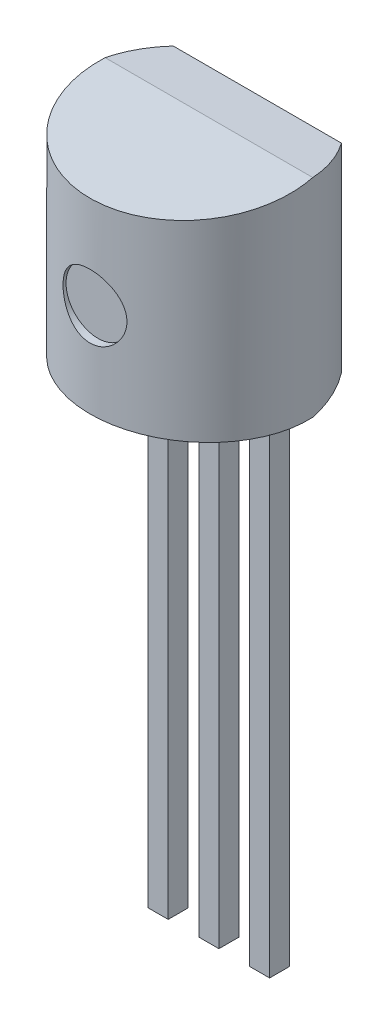
SolidWorks part; units mm, degrees
ref_plane "Front Plane" through (0, 0, 0) normal (0, 0, 1) x (1, 0, 0)
ref_plane "Top Plane" through (0, 0, 0) normal (0, 1, 0) x (1, 0, 0)
ref_plane "Right Plane" through (0, 0, 0) normal (1, 0, 0) x (0, 0, -1)
sketch "Sketch2" plane through (0, 0, 0) normal (0, 1, 0) x (1, 0, 0)
  line L0 (-2.6, 0) -> (2.6, 0) construction
  line L1 (-2.1054, 1.212) -> (2.1054, 1.212)
  line L2 (0, 0) -> (0, 1.212) construction
  arc A0 (-2.1054, 1.212) -> (2.1054, 1.212) centre (0, -0.354) ccw
  point P3 (0, 0)
  dimension "D1" = 4.19
  dimension "D2" = 5.2
  dimension "D3" = 2.27
extrude "Boss-Extrude1" add sketch "Sketch2" along normal mid plane 5.2
sketch "Sketch3" plane through (0, 2.6, 0) normal (0, 1, 0) x (1, 0, 0)
  line L0 (-2.6, 0) -> (2.6, 0) construction
  line L1 (-2.6, 0) -> (2.6, 0) construction
ref_plane "Plane1" through (0, 2.5803, -0.2257) normal (0, 0.9962, -0.0872) x (1, 0, 0)
ref_plane "Plane2" through (0, 2.5803, 0.2257) normal (0, 0.9962, 0.0872) x (1, 0, 0)
sketch "Sketch5" plane through (0, 2.5803, -0.2257) normal (0, 0.9962, -0.0872) x (1, 0, 0)
  line L1 (-4.9885, 2.0659) -> (6.8379, 2.0659)
  line L2 (-4.9885, 2.0659) -> (-4.9885, -3.5552)
  line L3 (-4.9885, -3.5552) -> (6.8379, -3.5552)
  line L4 (6.8379, 2.0659) -> (6.8379, -3.5552)
extrude "Cut-Extrude2" cut sketch "Sketch5" along normal through all
sketch "Sketch6" plane through (0, 2.5803, 0.2257) normal (0, 0.9962, 0.0872) x (1, 0, 0)
  line L1 (-5.588, 1.1618) -> (6.1027, 1.1618)
  line L2 (-5.588, 1.1618) -> (-5.588, -6.0928)
  line L3 (-5.588, -6.0928) -> (6.1027, -6.0928)
  line L4 (6.1027, 1.1618) -> (6.1027, -6.0928)
extrude "Cut-Extrude3" cut sketch "Sketch6" along normal blind 5.2
mirror "Mirror1" about plane through (0, 0, 0) normal (0, 1, 0) of "Cut-Extrude3", "Cut-Extrude2"
ref_plane "Plane3" through (0, -2.6, 0) normal (0, -1, 0) x (-1, 0, 0)
sketch "Sketch7" plane through (0, -2.6, 0) normal (0, -1, 0) x (-1, 0, 0)
  line L0 (-2.6, 0) -> (2.6, 0) construction
  line L1 (-1.52, 0) -> (-1.02, 0)
  line L2 (-1.52, 0) -> (-1.52, 0.5)
  line L3 (-1.52, 0.5) -> (-1.02, 0.5)
  line L4 (-1.02, 0) -> (-1.02, 0.5)
  line L5 (0, 0) -> (0, 0.5) construction
  line L6 (-0.25, 0) -> (0.25, 0)
  line L7 (-0.25, 0) -> (-0.25, 0.5)
  line L8 (-0.25, 0.5) -> (0.25, 0.5)
  line L9 (0.25, 0) -> (0.25, 0.5)
  line L10 (1.02, 0) -> (1.52, 0)
  line L11 (1.02, 0) -> (1.02, 0.5)
  line L12 (1.02, 0.5) -> (1.52, 0.5)
  line L13 (1.52, 0) -> (1.52, 0.5)
  line L14 (1.27, 0.5) -> (1.27, 0) construction
  line L15 (-1.27, 0.5) -> (-1.27, 0) construction
  dimension "D1" = 1.27
  dimension "D2" = 2.54
  dimension "D3" = 0.5
extrude "Boss-Extrude2" add sketch "Sketch7" along normal blind 12.7 and the other way up to body separate body
ref_plane "Plane4" through (0, 0, 2.978) normal (0, 0, 1) x (1, 0, 0)
sketch "Sketch8" plane through (0, 0, 2.978) normal (0, 0, 1) x (1, 0, 0)
  circle A0 centre (0, 0) radius 0.8
  dimension "D1" = 1.6
extrude "Cut-Extrude4" cut sketch "Sketch8" against normal blind 0.2
sketch "Sketch9" plane through (0, 0, -1.212) normal (0, 0, -1) x (-1, 0, 0)
  line L0 (-1.3031, 0.1784) -> (1.2996, 0.1784) construction
  line L1 (-1.3031, -0.7444) -> (1.2996, -0.7444) construction
  text T0 "LM35" font "Arial" height in points 2
  text T1 "DZ" font "Arial" height in points 2
split line "Split Line1"
